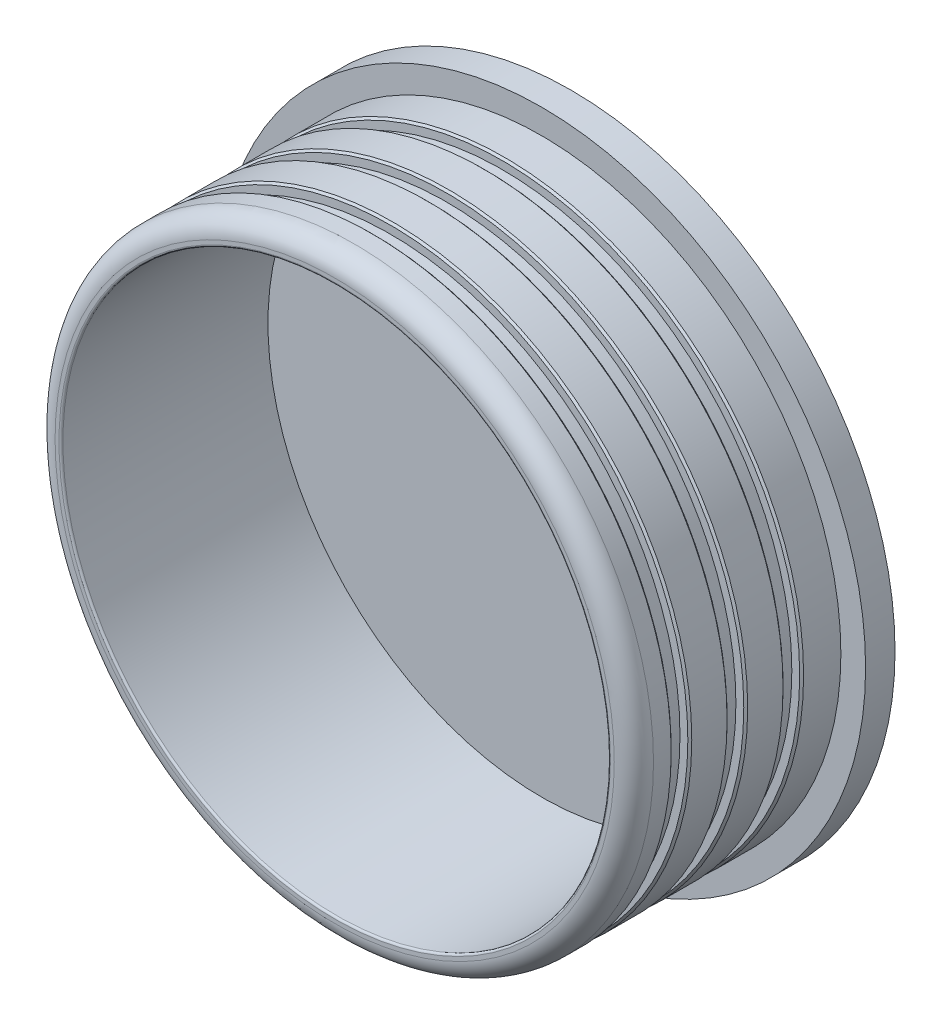
SolidWorks part; units mm, degrees
ref_plane "Front Plane" through (0, 0, 0) normal (0, 0, 1) x (1, 0, 0)
ref_plane "Top Plane" through (0, 0, 0) normal (0, 1, 0) x (1, 0, 0)
ref_plane "Right Plane" through (0, 0, 0) normal (1, 0, 0) x (0, 0, -1)
sketch "Sketch1" plane through (0, 0, 0) normal (0, 1, 0) x (1, 0, 0)
  line L0 (0, 0) -> (0, 70) construction
  line L1 (69.75, 0) -> (76.25, 0)
  line L2 (76.25, 0) -> (76.25, 10)
  line L3 (76.25, 10) -> (73.75, 10)
  line L4 (73.75, 10) -> (73.75, 14.25)
  line L5 (73.75, 14.25) -> (76.25, 14.25)
  line L6 (76.25, 14.25) -> (76.25, 24.25)
  line L7 (76.25, 24.25) -> (73.75, 24.25)
  line L8 (73.75, 24.25) -> (73.75, 28.5)
  line L9 (73.75, 28.5) -> (76.25, 28.5)
  line L10 (76.25, 28.5) -> (76.25, 38.5)
  line L11 (76.25, 38.5) -> (73.75, 38.5)
  line L12 (73.75, 38.5) -> (73.75, 42.75)
  line L13 (73.75, 42.75) -> (76.25, 42.75)
  line L14 (76.25, 42.75) -> (76.25, 52.75)
  line L15 (76.25, 52.75) -> (82.55, 52.75)
  line L16 (82.55, 52.75) -> (82.55, 60.25)
  line L17 (82.55, 60.25) -> (0, 60.25)
  line L18 (0, 60.25) -> (0, 52.75)
  line L19 (0, 52.75) -> (69.75, 52.75)
  line L20 (69.75, 52.75) -> (69.75, 0)
  dimension "D1" = 82.55
  dimension "D2" = 7.5
  dimension "D3" = 76.25
  dimension "D4" = 4.25
  dimension "D5" = 2.5
  dimension "D6" = 52.75
  dimension "D7" = 52.75
  dimension "D8" = 6.5
  dimension "D9" = 10
  dimension "D10" = 70
revolve "Revolve1" add sketch "Sketch1" angle 360 about L0
chamfer "Chamfer1" distance 0.5 angle 45 6 edges at (76.25, 0, -10) (76.25, 0, -14.25) (76.25, 0, -24.25) (76.25, 0, -28.5) (76.25, 0, -42.75) (76.25, 0, -38.5)
fillet "Fillet1" radius 5 1 edges at (76.25, 0, 0)
fillet "Fillet2" radius 0.5 1 edges at (69.75, 0, 0)
